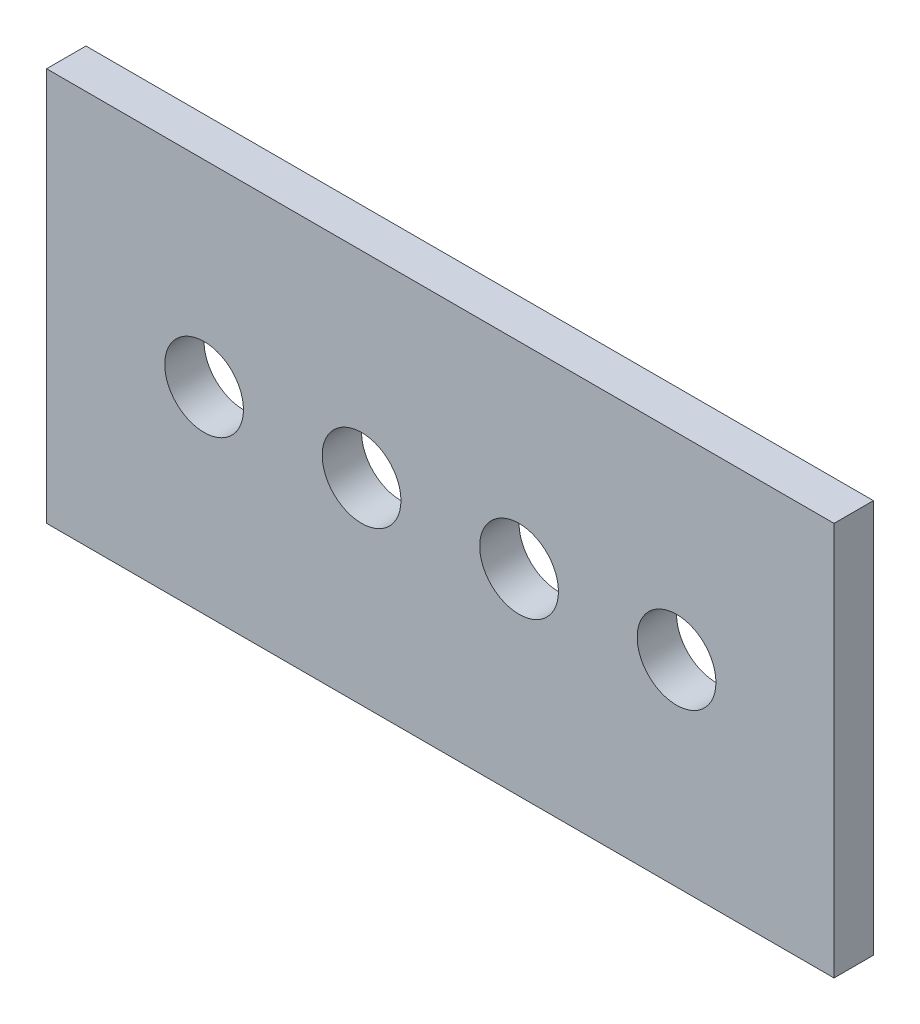
SolidWorks part; units mm, degrees
ref_plane "Front Plane" through (0, 0, 0) normal (0, 0, 1) x (1, 0, 0)
ref_plane "Top Plane" through (0, 0, 0) normal (0, 1, 0) x (1, 0, 0)
ref_plane "Right Plane" through (0, 0, 0) normal (1, 0, 0) x (0, 0, -1)
sketch "Sketch1" plane through (0, 0, 0) normal (0, 0, 1) x (1, 0, 0)
  line L1 (0, 0) -> (100, 0)
  line L2 (0, 0) -> (0, 50)
  line L3 (0, 50) -> (100, 50)
  line L4 (100, 0) -> (100, 50)
  circle A0 centre (20, 25) radius 5
  circle A1 centre (40, 25) radius 5
  circle A2 centre (60, 25) radius 5
  circle A3 centre (80, 25) radius 5
  point P7 (0, 25)
  dimension "D4" = 10
  dimension "D1" = 100
  dimension "D2" = 50
  dimension "D3" = 20
  dimension "D5" = 4
extrude "Boss-Extrude1" add sketch "Sketch1" along normal blind 5
